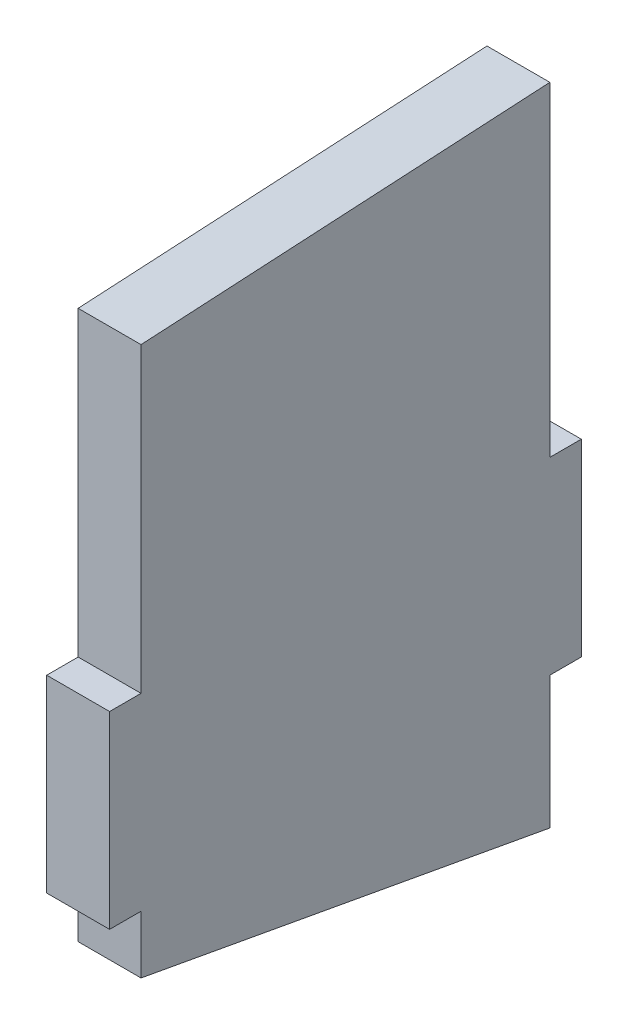
SolidWorks part; units mm, degrees
material "Pink Foam"
ref_plane "Front Plane" through (0, 0, 0) normal (0, 0, 1) x (1, 0, 0)
ref_plane "Top Plane" through (0, 0, 0) normal (0, 1, 0) x (1, 0, 0)
ref_plane "Right Plane" through (0, 0, 0) normal (1, 0, 0) x (0, 0, -1)
sketch "Sketch1" plane through (0, 0, 0) normal (1, 0, 0) x (0, 0, -1)
  line L0 (-82.55, 160.0689) -> (82.55, 169.2558)
  line L1 (-82.55, -203.2) -> (82.55, -203.2)
  line L2 (-82.55, -203.2) -> (-82.55, 203.2)
  line L3 (-82.55, 203.2) -> (82.55, 203.2)
  line L4 (82.55, -203.2) -> (82.55, 203.2)
  line L5 (-82.55, -203.2) -> (82.55, 203.2) construction
  line L6 (-82.55, 203.2) -> (82.55, -203.2) construction
  line L7 (-95.25, -38.1) -> (95.25, -38.1)
  line L8 (-95.25, -38.1) -> (-95.25, 38.1)
  line L9 (-95.25, 38.1) -> (95.25, 38.1)
  line L10 (95.25, -38.1) -> (95.25, 38.1)
  line L11 (-95.25, -38.1) -> (95.25, 38.1) construction
  line L12 (-95.25, 38.1) -> (95.25, -38.1) construction
  line L14 (-82.55, -61.4555) -> (82.55, -91.5455)
  point P0 (0, 0)
  point P6 (0, 0)
  dimension "D1" = 165.1
  dimension "D2" = 190.5
  dimension "D3" = 76.2
  dimension "D4" = 406.4
  dimension "D5" = 43.1311
  dimension "D6" = 33.9442
  dimension "D7" = 111.6545
  dimension "D8" = 221.5244
extrude "Boss-Extrude1" add sketch "Sketch1" along normal blind 25.4 contours L2 L9 L4 L0 | L7 L10 L9 L4 | L9 L2 L7 L4 | L9 L8 L7 L2 | L2 L14 L4 L7
